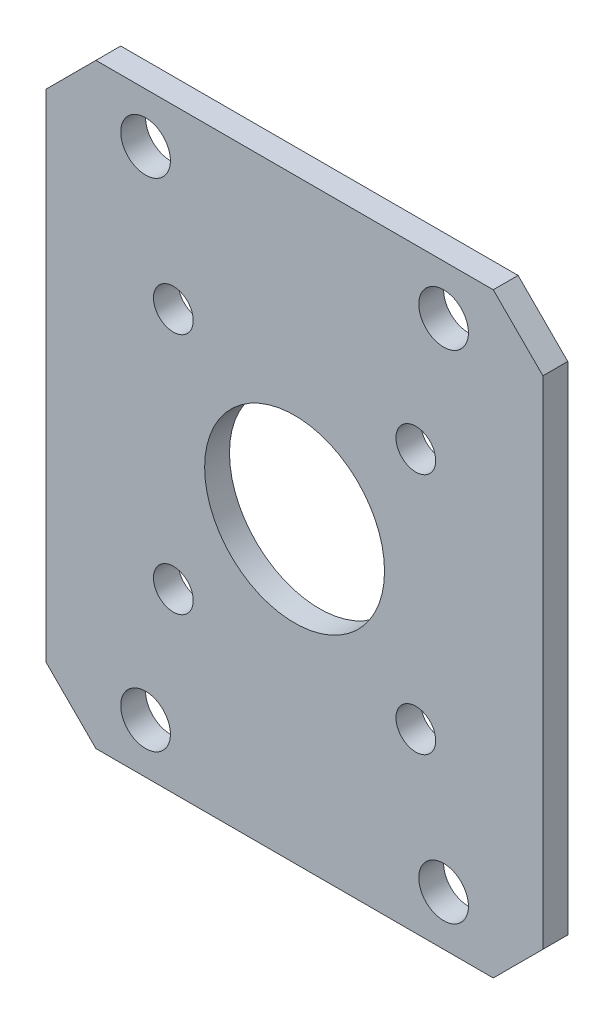
SolidWorks part; units mm, degrees
material "5052-O"
ref_plane "Front Plane" through (0, 0, 0) normal (0, 0, 1) x (1, 0, 0)
ref_plane "Top Plane" through (0, 0, 0) normal (0, 1, 0) x (1, 0, 0)
ref_plane "Right Plane" through (0, 0, 0) normal (1, 0, 0) x (0, 0, -1)
sketch "Sketch1" plane through (0, 0, 0) normal (0, 0, 1) x (1, 0, 0)
  line L1 (-31.75, -38.1) -> (31.75, -38.1)
  line L2 (-31.75, -38.1) -> (-31.75, 38.1)
  line L3 (-31.75, 38.1) -> (31.75, 38.1)
  line L4 (31.75, -38.1) -> (31.75, 38.1)
  line L5 (-31.75, -38.1) -> (31.75, 38.1) construction
  line L6 (-31.75, 38.1) -> (31.75, -38.1) construction
  point P0 (0, 0)
  dimension "D1" = 63.5
  dimension "D2" = 76.2
extrude "Boss-Extrude1" add sketch "Sketch1" along normal mid plane 3.175
sketch "Sketch2" plane through (0, 0, 1.5875) normal (0, 0, 1) x (1, 0, 0)
  line L1 (-19.05, -31.75) -> (19.05, -31.75) construction
  line L2 (-19.05, -31.75) -> (-19.05, 31.75) construction
  line L3 (-19.05, 31.75) -> (19.05, 31.75) construction
  line L4 (19.05, -31.75) -> (19.05, 31.75) construction
  line L5 (-19.05, -31.75) -> (19.05, 31.75) construction
  line L6 (-19.05, 31.75) -> (19.05, -31.75) construction
  circle A0 centre (-19.05, 31.75) radius 3.175
  circle A1 centre (19.05, 31.75) radius 3.175
  circle A2 centre (19.05, -31.75) radius 3.175
  circle A3 centre (-19.05, -31.75) radius 3.175
  point P0 (0, 0)
  dimension "D1" = 6.35
  dimension "D2" = 38.1
  dimension "D3" = 63.5
extrude "Cut-Extrude1" cut sketch "Sketch2" against normal through all
sketch "Sketch3" plane through (0, 0, 1.5875) normal (0, 0, 1) x (1, 0, 0)
  line L1 (-15.5, -15.5) -> (15.5, -15.5) construction
  line L2 (-15.5, -15.5) -> (-15.5, 15.5) construction
  line L3 (-15.5, 15.5) -> (15.5, 15.5) construction
  line L4 (15.5, -15.5) -> (15.5, 15.5) construction
  line L5 (-15.5, -15.5) -> (15.5, 15.5) construction
  line L6 (-15.5, 15.5) -> (15.5, -15.5) construction
  circle A0 centre (-15.5, 15.5) radius 2.54
  circle A1 centre (15.5, 15.5) radius 2.54
  circle A2 centre (15.5, -15.5) radius 2.54
  circle A3 centre (-15.5, -15.5) radius 2.54
  point P0 (0, 0)
  dimension "D1" = 5.08
  dimension "D2" = 31
extrude "Cut-Extrude2" cut sketch "Sketch3" against normal through all
chamfer "Chamfer1" distance 6.35 angle 45 4 edges at (-31.75, -38.1, 0) (31.75, -38.1, 0) (31.75, 38.1, 0) (-31.75, 38.1, 0)
sketch "Sketch4" plane through (0, 0, 1.5875) normal (0, 0, 1) x (1, 0, 0)
  circle A0 centre (0, 0) radius 11.5
  dimension "D1" = 23
extrude "Cut-Extrude3" cut sketch "Sketch4" against normal through all
